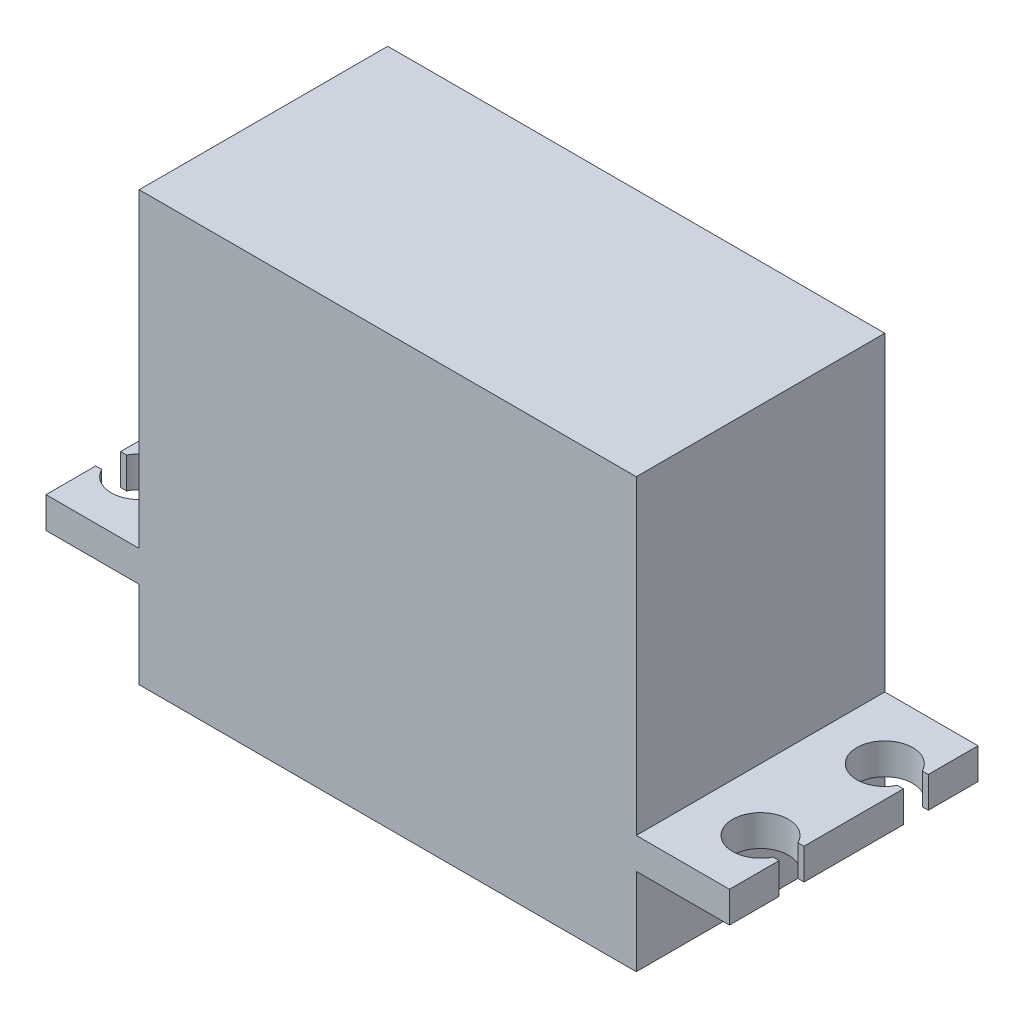
SolidWorks part; units mm, degrees
ref_plane "Front Plane" through (0, 0, 0) normal (0, 0, 1) x (1, 0, 0)
ref_plane "Top Plane" through (0, 0, 0) normal (0, 1, 0) x (1, 0, 0)
ref_plane "Right Plane" through (0, 0, 0) normal (1, 0, 0) x (0, 0, -1)
sketch "Sketch1" plane through (0, 0, 0) normal (0, 1, 0) x (1, 0, 0)
  line L1 (-40, 10) -> (0, 10)
  line L2 (-40, 10) -> (-40, -10)
  line L3 (-40, -10) -> (0, -10)
  line L4 (0, 10) -> (0, -10)
  point P4 (0, 0)
  dimension "D1" = 20
  dimension "D2" = 40
extrude "Boss-Extrude1" add sketch "Sketch1" along normal blind 25 and the other way blind 9.5
sketch "Sketch2" plane through (0, 0, 0) normal (0, 1, 0) x (1, 0, 0)
  line L0 (-40, 10) -> (-47.5, 10)
  line L1 (-40, 10) -> (-40, -10) construction
  line L2 (-40, -10) -> (-47.5, -10)
  line L3 (-47.5, -10) -> (-47.5, -6)
  line L4 (0, 0) -> (-48.3069, 0) construction
  line L5 (0, -10) -> (0, 10) construction
  line L6 (-47.0156, -6) -> (-47.5, -6)
  line L7 (-47.0156, -4) -> (-47.5, -4)
  line L8 (-47.0156, 4) -> (-47.5, 4)
  line L9 (-47.0156, 6) -> (-47.5, 6)
  line L10 (-45, -5) -> (-48.8069, -5) construction
  line L11 (-45, 5) -> (-48.3069, 5) construction
  line L12 (-47.5, 6) -> (-47.5, 10)
  line L13 (-47.5, -4) -> (-47.5, 4)
  line L14 (-20, 10) -> (-20, -11.2967) construction
  line L15 (0, 10) -> (-40, 10) construction
  line L16 (5, 5) -> (8.3069, 5) construction
  line L17 (5, -5) -> (8.8069, -5) construction
  line L18 (7.5, -4) -> (7.5, 4)
  line L19 (7.5, 6) -> (7.5, 10)
  line L20 (7.0156, 6) -> (7.5, 6)
  line L21 (7.0156, 4) -> (7.5, 4)
  line L22 (7.0156, -4) -> (7.5, -4)
  line L23 (7.0156, -6) -> (7.5, -6)
  line L24 (7.5, -10) -> (7.5, -6)
  line L25 (0, -10) -> (7.5, -10)
  line L26 (0, 10) -> (7.5, 10)
  line L27 (-40, 10) -> (-40, -10)
  line L28 (0, 10) -> (0, -10)
  arc A0 (-47.0156, 4) -> (-47.0156, 6) centre (-45, 5) ccw
  arc A1 (-47.0156, -6) -> (-47.0156, -4) centre (-45, -5) ccw
  arc A2 (7.0156, -6) -> (7.0156, -4) centre (5, -5) cw
  arc A3 (7.0156, 4) -> (7.0156, 6) centre (5, 5) cw
  point P24 (-47.2578, 6)
  point P25 (-47.2578, 4)
  dimension "D3" = 4.5
  dimension "D4" = 4.5
  dimension "D1" = 10
  dimension "D2" = 5
  dimension "D5" = 5
  dimension "D6" = 7.5
  dimension "D7" = 2
  dimension "D8" = 2
  dimension "D9" = 1
  dimension "D10" = 1
extrude "Boss-Extrude2" add sketch "Sketch2" against normal blind 2.5
sketch "Sketch3" plane through (0, -9.5, 0) normal (0, -1, 0) x (-1, 0, 0)
  line L0 (40, 0) -> (0, 0) construction
  line L1 (40, 10) -> (40, -10) construction
  circle A0 centre (28.5, 0) radius 3
  dimension "D1" = 6
  dimension "D2" = 11.5
extrude "Boss-Extrude3" add sketch "Sketch3" along normal blind 6
